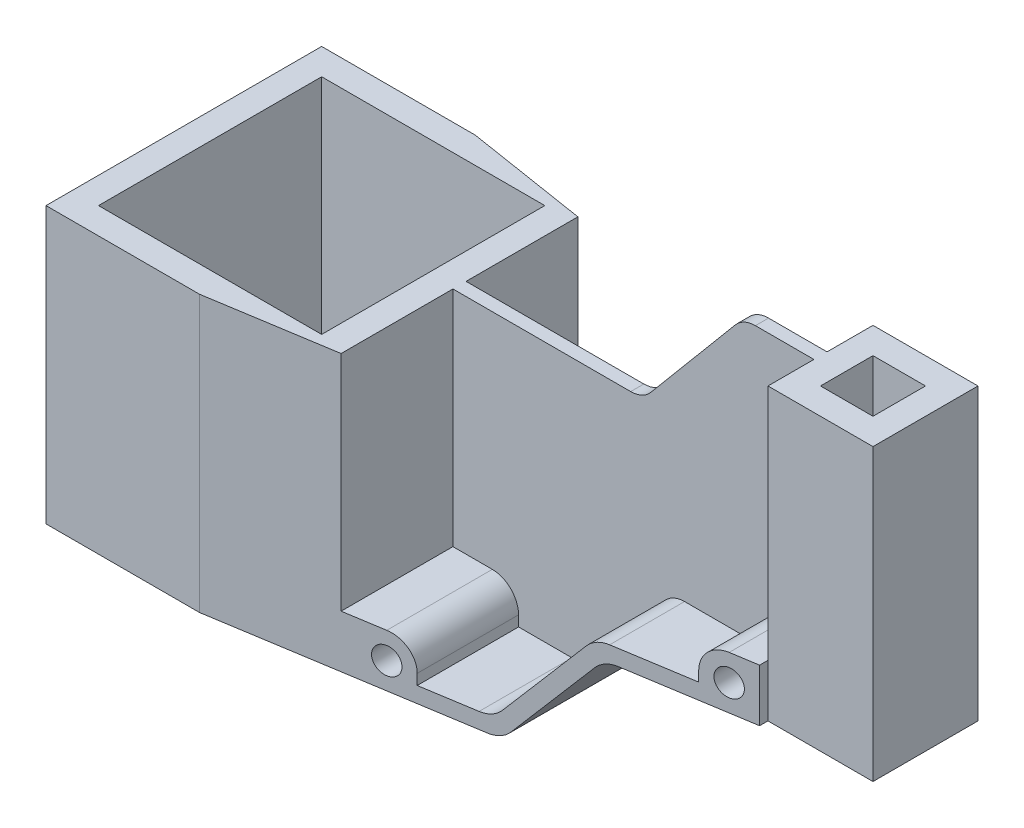
SolidWorks part; units mm, degrees
material "1060 Alloy"
ref_plane "Front Plane" through (0, 0, 0) normal (0, 0, 1) x (1, 0, 0)
ref_plane "Top Plane" through (0, 0, 0) normal (0, 1, 0) x (1, 0, 0)
ref_plane "Right Plane" through (0, 0, 0) normal (1, 0, 0) x (0, 0, -1)
sketch "Sketch1" plane through (0, 0, 0) normal (0, 1, 0) x (1, 0, 0)
  line L1 (0, 0) -> (-282.5, 0)
  line L2 (0, 0) -> (0, -105)
  line L3 (0, -105) -> (-282.5, -105)
  line L4 (-282.5, 0) -> (-282.5, -105)
  dimension "D1" = 282.5
  dimension "D2" = 105
extrude "Boss-Extrude1" add sketch "Sketch1" along normal blind 150.5
sketch "Sketch2" plane through (0, 150.5, 0) normal (0, 1, 0) x (1, 0, 0)
  line L0 (-282.5, 0) -> (-282.5, -105) construction
  line L1 (-282.5, 0) -> (-127.5, 0)
  line L2 (-282.5, 0) -> (-282.5, -105)
  line L3 (-282.5, -105) -> (-127.5, -105)
  line L4 (-127.5, 0) -> (-127.5, -105)
  line L5 (-282.5, -105) -> (0, -105) construction
  dimension "D1" = 155
extrude "Cut-Extrude1" cut sketch "Sketch2" against normal blind 45.5
sketch "Sketch3" plane through (0, 105, 0) normal (0, 1, 0) x (1, 0, 0)
  line L0 (-282.5, -52.5) -> (-123.2198, -52.5) construction
  line L1 (-282.5, 0) -> (-282.5, -105) construction
  line L2 (-127.5, -105) -> (-127.5, 0) construction
  line L3 (-127.5, -55) -> (-177.5, -55)
  line L4 (-127.5, -55) -> (-127.5, -105)
  line L5 (-127.5, -105) -> (-177.5, -105)
  line L6 (-177.5, -55) -> (-177.5, -105)
  line L7 (-282.5, -105) -> (-127.5, -105) construction
  line L8 (-127.5, -50) -> (-127.5, 0)
  line L9 (-127.5, 0) -> (-177.5, 0)
  line L10 (-177.5, -50) -> (-177.5, 0)
  line L11 (-127.5, -50) -> (-177.5, -50)
  dimension "D1" = 2.5
  dimension "D2" = 50
extrude "Cut-Extrude2" cut sketch "Sketch3" against normal blind 85
sketch "Sketch4" plane through (0, 0, 105) normal (0, 0, 1) x (1, 0, 0)
  line L0 (-152.5, 6) -> (-127.5, 6)
  line L1 (-282.5, 0) -> (0, 0) construction
  line L2 (-177.5, 20) -> (-162.5, 20)
  line L3 (-177.5, 20) -> (-127.5, 20) construction
  line L4 (-282.5, 105) -> (-282.5, 0) construction
  line L5 (-152.5, 10) -> (-152.5, 6)
  line L6 (-177.5, 20) -> (-177.5, 105)
  line L7 (-177.5, 105) -> (-127.5, 105)
  line L8 (-127.5, 105) -> (-127.5, 6)
  circle A0 centre (-162.5, 10) radius 5
  arc A1 (-162.5, 20) -> (-152.5, 10) centre (-162.5, 10) cw
  dimension "D3" = 10
  dimension "D1" = 6
  dimension "D2" = 120
  dimension "D4" = 155
extrude "Cut-Extrude3" cut sketch "Sketch4" against normal blind 50
sketch "Sketch5" plane through (0, 0, 0) normal (0, 0, -1) x (-1, 0, 0)
  line L0 (127.5, 105) -> (177.5, 105)
  line L1 (177.5, 105) -> (177.5, 20)
  line L2 (177.5, 20) -> (162.5, 20)
  line L3 (152.5, 10) -> (152.5, 6)
  line L4 (152.5, 6) -> (127.5, 6)
  line L5 (127.5, 6) -> (127.5, 105)
  arc A0 (162.5, 20) -> (152.5, 10) centre (162.5, 10) ccw
  circle A1 centre (162.5, 10) radius 5
extrude "Cut-Extrude4" cut sketch "Sketch5" against normal blind 50
sketch "Sketch6" plane through (0, 0, 105) normal (0, 0, 1) x (1, 0, 0)
  line L0 (-127.5, 6) -> (-78.3718, 64.5487)
  line L1 (-152.5, 6) -> (-127.5, 6) construction
  line L2 (-91.1382, 40) -> (-124.7022, 0)
  line L3 (-282.5, 0) -> (0, 0) construction
  line L4 (-91.1382, 40) -> (0, 40)
  line L5 (0, 150.5) -> (0, 0) construction
  line L6 (0, 40) -> (0, 0)
  line L7 (0, 0) -> (-124.7022, 0)
  line M13 (-282.5, 0) -> (0, 0)
  line M14 (0, 0) -> (0, 150.5)
  dimension "D1" = 130
  dimension "D2" = 6
  dimension "D3" = 40
extrude "Cut-Extrude5" cut sketch "Sketch6" against normal through all contours L4 L2 M13 M14
sketch "Sketch7" plane through (0, 0, 105) normal (0, 0, 1) x (1, 0, 0)
  line L0 (-93.936, 46) -> (-60, 46)
  line L1 (-127.5, 6) -> (-78.3718, 64.5487) construction
  line L2 (0, 150.5) -> (0, 40) construction
  line L3 (-91.1382, 40) -> (0, 40) construction
  line L4 (-50, 60) -> (-40, 60)
  line L5 (-40, 60) -> (-40, 150.5)
  line L6 (-127.5, 150.5) -> (0, 150.5) construction
  line L7 (-60, 50) -> (-60, 46)
  line L8 (-105.1306, 105) -> (-66.9515, 150.5)
  line L9 (-91.1382, 40) -> (-124.7022, 0) construction
  line L10 (-127.5, 105) -> (-105.1306, 105)
  line L11 (-105.1306, 105) -> (-66.9515, 150.5)
  line L12 (-127.5, 150.5) -> (-127.5, 105)
  line L13 (-127.5, 150.5) -> (-66.9515, 150.5)
  circle A1 centre (-50, 50) radius 5
  arc A2 (-50, 60) -> (-60, 50) centre (-50, 50) ccw
  line M8 (0, 150.5) -> (-127.5, 150.5)
  line M9 (-127.5, 150.5) -> (-127.5, 6)
  dimension "D5" = 10
  dimension "D6" = 52.5
  dimension "D1" = 6
  dimension "D2" = 20
  dimension "D3" = 50
  dimension "D4" = 40
extrude "Cut-Extrude6" cut sketch "Sketch7" against normal through all contours L10 L8 M9 M8
sketch "Sketch8" plane through (0, 0, 105) normal (0, 0, 1) x (1, 0, 0)
  line L0 (-40, 150.5) -> (-66.9515, 150.5)
  line L1 (-66.9515, 150.5) -> (-105.1306, 105)
  line L2 (-105.1306, 105) -> (-127.5, 105)
  line L3 (-127.5, 105) -> (-127.5, 6)
  line L4 (-127.5, 6) -> (-93.936, 46)
  line L5 (-93.936, 46) -> (-60, 46)
  line L6 (-60, 46) -> (-60, 50)
  line L7 (-50, 60) -> (-40, 60)
  line L8 (-40, 60) -> (-40, 150.5)
  arc A0 (-60, 50) -> (-50, 60) centre (-50, 50) cw
  circle A1 centre (-50, 50) radius 5
extrude "Cut-Extrude7" cut sketch "Sketch8" against normal blind 50
sketch "Sketch9" plane through (0, 0, 0) normal (0, 0, -1) x (-1, 0, 0)
  line L0 (0, 150.5) -> (40, 150.5)
  line L1 (40, 150.5) -> (40, 60)
  line L2 (40, 60) -> (50, 60)
  line L3 (60, 50) -> (60, 46)
  line L4 (60, 46) -> (93.936, 46)
  line L5 (93.936, 46) -> (127.5, 6)
  line L6 (127.5, 6) -> (127.5, 150.5)
  line L7 (127.5, 150.5) -> (40, 150.5)
  arc A0 (50, 60) -> (60, 50) centre (50, 50) cw
  circle A1 centre (50, 50) radius 5
  line M2 (127.5, 105) -> (105.1306, 105)
  line M3 (105.1306, 105) -> (66.9515, 150.5)
  line M4 (66.9515, 150.5) -> (0, 150.5)
  line M16 (127.5, 6) -> (127.5, 105)
extrude "Cut-Extrude8" cut sketch "Sketch9" against normal blind 50 contours L2 A0 L3 L4 L5 L1 M16 M2 M3 M4
sketch "Sketch10" plane through (0, 0, 0) normal (0, 0, -1) x (-1, 0, 0)
  circle A0 centre (50, 50) radius 5 construction
  circle A1 centre (50, 50) radius 5
extrude "Cut-Extrude9" cut sketch "Sketch10" against normal through all
sketch "Sketch11" plane through (0, 0, 0) normal (0, 0, -1) x (-1, 0, 0)
  circle A0 centre (162.5, 10) radius 5 construction
  circle A1 centre (162.5, 10) radius 5
extrude "Cut-Extrude10" cut sketch "Sketch11" against normal through all
sketch "Sketch12" plane through (0, 105, 0) normal (0, 1, 0) x (1, 0, 0)
  line L0 (-282.5, 0) -> (-282.5, -105) construction
  line L1 (-272.5, -10) -> (-187.5, -10)
  line L2 (-272.5, -10) -> (-272.5, -95)
  line L3 (-272.5, -95) -> (-187.5, -95)
  line L4 (-187.5, -10) -> (-187.5, -95)
  line L5 (-177.5, 0) -> (-177.5, -50) construction
  line L6 (-177.5, 0) -> (-282.5, 0) construction
  line L7 (-282.5, -105) -> (-177.5, -105) construction
  dimension "D1" = 10
  dimension "D2" = 10
  dimension "D3" = 10
  dimension "D4" = 10
extrude "Cut-Extrude11" cut sketch "Sketch12" against normal through all
sketch "Sketch13" plane through (0, 150.5, 0) normal (0, 1, 0) x (1, 0, 0)
  line L0 (-40, -72.5) -> (0, -72.5)
  line L1 (-40, -55) -> (-40, -105) construction
  line L2 (0, -105) -> (0, 0) construction
  line L3 (-40, -105) -> (0, -105) construction
  line L4 (-40, -32.5) -> (0, -32.5)
  line L5 (-40, -50) -> (-40, 0) construction
  line L6 (0, 0) -> (-40, 0) construction
  line L7 (-40, -32.5) -> (-40, 0)
  line L8 (-40, 0) -> (-50, 0) construction
  line L9 (-40, 0) -> (0, 0)
  line L10 (0, 0) -> (0, -32.5)
  line L11 (0, -72.5) -> (0, -105)
  line L12 (0, -105) -> (-40, -105)
  line L13 (-40, -105) -> (-40, -72.5)
  dimension "D1" = 32.5
  dimension "D2" = 32.5
extrude "Cut-Extrude12" cut sketch "Sketch13" against normal through all
sketch "Sketch14" plane through (0, 150.5, 0) normal (0, 1, 0) x (1, 0, 0)
  line L0 (-40, -32.5) -> (0, -32.5) construction
  line L1 (-30, -42.5) -> (-10, -42.5)
  line L2 (-30, -42.5) -> (-30, -62.5)
  line L3 (-30, -62.5) -> (-10, -62.5)
  line L4 (-10, -42.5) -> (-10, -62.5)
  line L5 (0, -72.5) -> (-40, -72.5) construction
  line L6 (0, -72.5) -> (0, -32.5) construction
  line L7 (-40, -50) -> (-40, -32.5) construction
  dimension "D1" = 10
  dimension "D2" = 10
  dimension "D3" = 10
  dimension "D4" = 10
extrude "Cut-Extrude13" cut sketch "Sketch14" against normal through all
sketch "Sketch15" plane through (0, 105, 0) normal (0, 1, 0) x (1, 0, 0)
  line L0 (-230, 0) -> (-230, -105) construction
  line L1 (-177.5, 0) -> (-282.5, 0) construction
  line L2 (-282.5, -105) -> (-177.5, -105) construction
  line L3 (-224, 0) -> (-224, -105) construction
  line L4 (-20, -32.5) -> (-20, -72.5) construction
  line L5 (-40, -32.5) -> (0, -32.5) construction
  line L6 (0, -72.5) -> (-40, -72.5) construction
  line L7 (-224, 0) -> (-20, -32.5)
  line L8 (-20, -32.5) -> (-20, 0)
  line L9 (-20, 0) -> (-224, 0)
  line L10 (-224, -105) -> (-20, -72.5)
  line L11 (-20, -72.5) -> (-20, -105)
  line L12 (-20, -105) -> (-224, -105)
  dimension "D1" = 6
extrude "Cut-Extrude14" cut sketch "Sketch15" against normal through all
fillet "Fillet1" radius 10 4 edges at (-127.5, 6, 32.6869) (-127.5, 6, 72.3131) (-93.936, 46, 35.3605) (-93.936, 46, 69.6395)
fillet "Fillet2" radius 10 2 edges at (-91.1382, 40, 52.5) (-124.7022, 0, 52.5)
fillet "Fillet3" radius 10 2 edges at (-105.1306, 105, 52.5) (-66.9515, 150.5, 52.5)
